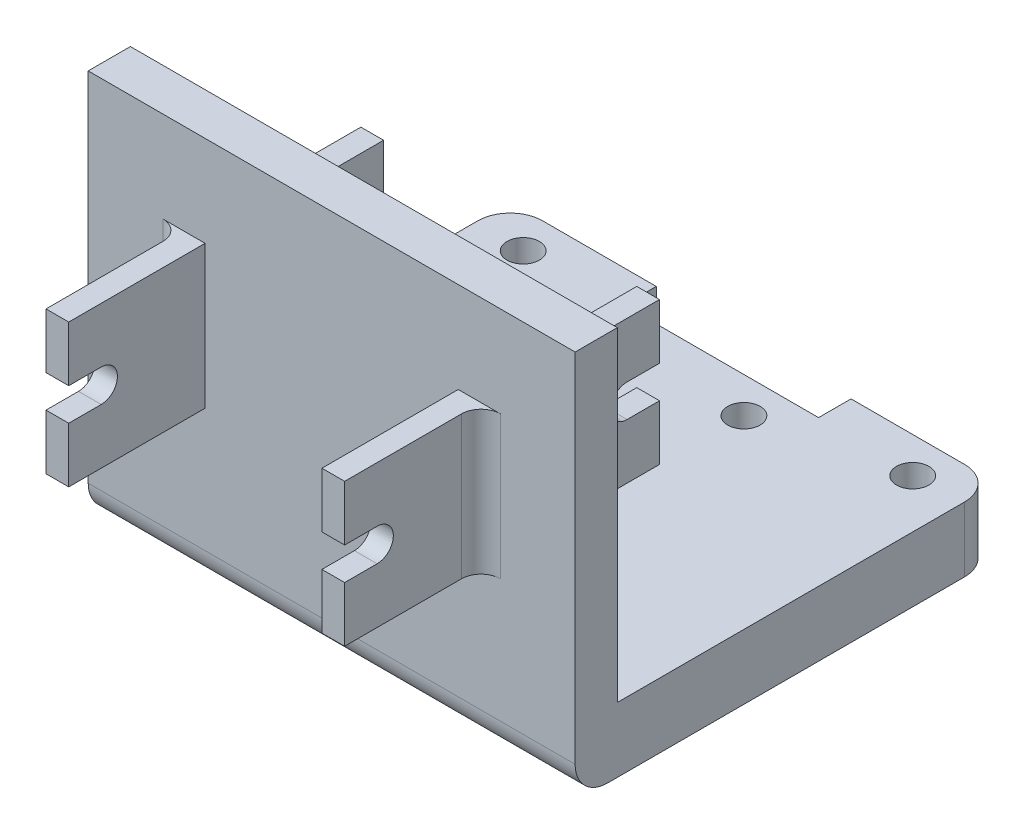
SolidWorks part; units mm, degrees
ref_plane "Front Plane" through (0, 0, 0) normal (0, 0, 1) x (1, 0, 0)
ref_plane "Top Plane" through (0, 0, 0) normal (0, 1, 0) x (1, 0, 0)
ref_plane "Right Plane" through (0, 0, 0) normal (1, 0, 0) x (0, 0, -1)
sketch "Sketch1" plane through (0, 0, 0) normal (0, 1, 0) x (1, 0, 0)
  line L1 (-37.5, -27.5) -> (37.5, -27.5)
  line L2 (-37.5, -27.5) -> (-37.5, 27.5)
  line L3 (-37.5, 27.5) -> (37.5, 27.5)
  line L4 (37.5, -27.5) -> (37.5, 27.5)
  line L5 (-37.5, -27.5) -> (37.5, 27.5) construction
  line L6 (-37.5, 27.5) -> (37.5, -27.5) construction
  circle A0 centre (-30, 22) radius 2.5
  circle A1 centre (30, 22) radius 2.5
  circle A2 centre (0, -18) radius 2.5
  point P0 (0, 0)
  dimension "D3" = 5
  dimension "D4" = 5
  dimension "D5" = 5
  dimension "D1" = 75
  dimension "D2" = 55
  dimension "D6" = 7.5
  dimension "D7" = 7.5
  dimension "D8" = 30
  dimension "D9" = 40
extrude "Boss-Extrude1" add sketch "Sketch1" along normal blind 10 contours L3 L4 L1 L2
sketch "Sketch7" plane through (0, 0, 0) normal (0, 1, 0) x (1, 0, 0)
  line L5 (-37.5, -27.5) -> (37.5, -27.5)
  line L6 (-37.5, -27.5) -> (-37.5, -37.5)
  line L7 (-37.5, -37.5) -> (37.5, -37.5)
  line L8 (37.5, -27.5) -> (37.5, -37.5)
  dimension "D1" = 10
  dimension "D2" = 75
extrude "Boss-Extrude2" add sketch "Sketch7" along normal blind 60
sketch "Sketch9" plane through (0, 60, 0) normal (0, 1, 0) x (1, 0, 0)
  line L0 (37.5, -37.5) -> (37.5, -27.5) construction
  line L1 (-37.5, -27.5) -> (37.5, -27.5)
  line L2 (-37.5, -27.5) -> (-37.5, -31)
  line L3 (-37.5, -31) -> (37.5, -31)
  line L4 (37.5, -27.5) -> (37.5, -31)
  dimension "D1" = 3.5
extrude "Cut-Extrude5" cut sketch "Sketch9" against normal blind 50
fillet "Fillet3" radius 5 1 edges at (0, 0, 37.5)
fillet "Fillet4" radius 5 2 edges at (37.5, 5, -27.5) (-37.5, 5, -27.5)
sketch "Sketch10" plane through (0, 0, 37.5) normal (0, 0, 1) x (1, 0, 0)
  line L1 (-23, 50) -> (23, 50)
  line L2 (-23, 50) -> (-23, 20)
  line L3 (-23, 20) -> (23, 20)
  line L4 (23, 50) -> (23, 20)
  line L5 (-37.5, 60) -> (-37.5, 5) construction
  line L6 (-37.5, 60) -> (37.5, 60) construction
  point P6 (0, 50)
  dimension "D1" = 30
  dimension "D2" = 46
  dimension "D3" = 37.5
  dimension "D4" = 10
extrude "Boss-Extrude3" add sketch "Sketch10" along normal blind 21
sketch "Sketch11" plane through (0, 50, 0) normal (0, 1, 0) x (1, 0, 0)
  line L0 (-37.5, -37.5) -> (37.5, -37.5) construction
  line L1 (-18, -37.5) -> (18, -37.5)
  line L2 (-18, -37.5) -> (-18, -53.5)
  line L3 (-18, -53.5) -> (18, -53.5)
  line L4 (18, -37.5) -> (18, -53.5)
  line L5 (-23, -58.5) -> (-23, -37.5) construction
  point P6 (0, -37.5)
  dimension "D1" = 36
  dimension "D2" = 23
  dimension "D3" = 16
extrude "Cut-Extrude6" cut sketch "Sketch11" against normal through all
sketch "Sketch12" plane through (0, 0, 31) normal (0, 0, -1) x (-1, 0, 0)
  line L1 (-23, 50) -> (23, 50)
  line L2 (-23, 50) -> (-23, 20)
  line L3 (-23, 20) -> (23, 20)
  line L4 (23, 50) -> (23, 20)
  line L6 (37.5, 60) -> (-37.5, 60) construction
  line L8 (-37.5, 10) -> (-37.5, 60) construction
  point P8 (0, 50)
  dimension "D1" = 46
  dimension "D2" = 30
  dimension "D3" = 10
  dimension "D4" = 37.5
extrude "Boss-Extrude4" add sketch "Sketch12" along normal blind 21
sketch "Sketch14" plane through (0, 50, 0) normal (0, 1, 0) x (1, 0, 0)
  line L0 (-23, -31) -> (23, -31) construction
  line L1 (-18, -31) -> (18, -31)
  line L2 (-18, -31) -> (-18, -15)
  line L3 (-18, -15) -> (18, -15)
  line L4 (18, -31) -> (18, -15)
  line L5 (-23, -10) -> (-23, -31) construction
  dimension "D1" = 36
  dimension "D2" = 5
  dimension "D3" = 16
extrude "Cut-Extrude7" cut sketch "Sketch14" against normal up to next
sketch "Sketch15" plane through (0, 0, 0) normal (0, -1, 0) x (1, 0, 0)
  line L0 (-15, -22.5) -> (-3, -22.5)
  line L1 (-15, -22.5) -> (-15, -27.5)
  line L2 (32.5, -27.5) -> (-32.5, -27.5) construction
  line L3 (15, -22.5) -> (15, -27.5)
  line L4 (-3, -22.5) -> (-3, -27.5)
  line L5 (3, -22.5) -> (3, -27.5)
  line L6 (-15, -27.5) -> (-3, -27.5)
  line L7 (3, -27.5) -> (15, -27.5)
  line L8 (3, -22.5) -> (15, -22.5)
  circle A0 centre (-30, -22) radius 2.5 construction
  circle A1 centre (30, -22) radius 2.5 construction
  point P14 (0, -27.5)
  dimension "D1" = 15
  dimension "D2" = 5
  dimension "D3" = 3
  dimension "D4" = 3
  dimension "D5" = 15
extrude "Boss-Extrude5" add sketch "Sketch15" along normal blind 20
sketch "Sketch16" plane through (0, 50, 0) normal (0, 1, 0) x (1, 0, 0)
  line L0 (-19.5, -31) -> (-19.5, -12.8854)
  line L1 (-23, -31) -> (-18, -31) construction
  line L2 (-19.5, -12.8854) -> (-19.5, -10)
  line L3 (-23, -10) -> (23, -10) construction
  line L4 (-19.5, -10) -> (19.5, -9.8969)
  line L5 (19.5, -9.8969) -> (19.5, -31)
  line L6 (23, -10) -> (23, -31) construction
  line L7 (19.5, -31) -> (-19.5, -31)
  line L8 (-23, -10) -> (-23, -31) construction
  line L9 (-33.2343, -34.25) -> (29.1707, -34.25)
  line L10 (-37.5, -31) -> (37.5, -31) construction
  line L14 (19.5, -58.6031) -> (19.5, -37.5)
  line L15 (-19.5, -58.5) -> (19.5, -58.6031)
  line L16 (-19.5, -55.6146) -> (-19.5, -58.5)
  line L17 (-19.5, -37.5) -> (-19.5, -55.6146)
  line L18 (19.5, -37.5) -> (-19.5, -37.5)
  dimension "D1" = 3.5
  dimension "D2" = 21.1031
  dimension "D3" = 3.5
  dimension "D4" = 3.25
extrude "Cut-Extrude9" cut sketch "Sketch16" along direction (0, -1, 0) on the side against the normal up to next (30 mm away) contours L14 L18 L17 L16 L15 | L7 L0 L2 L4 L5
sketch "Sketch17" plane through (-23, 0, 0) normal (-1, 0, 0) x (0, 0, 1)
  line L0 (10, 24) -> (31, 24)
  line L1 (10, 20) -> (10, 50) construction
  line L2 (31, 20) -> (31, 50) construction
  line L3 (10, 46) -> (31, 46)
  line L4 (10, 50) -> (31, 50) construction
  line L5 (10, 20) -> (31, 20) construction
  line L6 (15, 37.5) -> (10, 37.5)
  line L7 (15, 32.5) -> (10, 32.5)
  line L8 (10, 37.5) -> (10, 32.5)
  line L9 (10, 46) -> (10, 50)
  line L10 (10, 50) -> (31, 50)
  line L11 (31, 10) -> (31, 60) construction
  line L12 (10, 50) -> (31, 50) construction
  line L13 (31, 50) -> (31, 46)
  line L14 (31, 24) -> (31, 20)
  line L15 (31, 20) -> (10, 20)
  line L16 (10, 20) -> (10, 24)
  line L17 (34.25, 60) -> (34.25, 0)
  line L18 (37.5, 60) -> (31, 60) construction
  line L19 (37.5, 24) -> (37.5, 20)
  line L20 (37.5, 20) -> (58.5, 20)
  line L21 (58.5, 20) -> (58.5, 24)
  line L22 (58.5, 24) -> (37.5, 24)
  line L23 (58.5, 37.5) -> (58.5, 32.5)
  line L24 (53.5, 32.5) -> (58.5, 32.5)
  line L25 (53.5, 37.5) -> (58.5, 37.5)
  line L26 (58.5, 46) -> (58.5, 50)
  line L27 (58.5, 50) -> (37.5, 50)
  line L28 (37.5, 50) -> (37.5, 46)
  line L29 (58.5, 46) -> (37.5, 46)
  arc A0 (15, 32.5) -> (15, 37.5) centre (15, 35) ccw
  arc A1 (53.5, 32.5) -> (53.5, 37.5) centre (53.5, 35) cw
  line M14 (31, 20) -> (31, 50)
  line M15 (31, 50) -> (10, 50)
  line M16 (10, 50) -> (10, 20)
  line M17 (10, 20) -> (31, 20)
  dimension "D3" = 5
  dimension "D1" = 4
  dimension "D2" = 4
  dimension "D4" = 5
  dimension "D5" = 15
extrude "Cut-Extrude10" cut sketch "Sketch17" against normal through all contours L29 L26 L27 L28 | A1 L24 L23 L25 | L21 L22 L19 L20 | L3 M16 M14 M15 | L7 A0 L6 M16 | L0 M16 M17 M14
fillet "Fillet5" radius 3 4 edges at (-23, 35, 37.5) (23, 35, 37.5) (23, 35, 31) (-23, 35, 31)
sketch "Sketch18" plane through (0, 0, -27.5) normal (0, 0, -1) x (-1, 0, 0)
  line L0 (-15, -20) -> (-15, 10)
  line L1 (-32.5, 10) -> (32.5, 10) construction
  line L2 (15, -20) -> (15, 10)
  line L3 (15, 10) -> (-15, 10)
  line L4 (-15, -20) -> (15, -20)
extrude "Cut-Extrude11" cut sketch "Sketch18" against normal blind 5
sketch "Sketch19" plane through (0, 10, 0) normal (0, 1, 0) x (1, 0, 0)
  line L0 (-15, 22.5) -> (-15, 8.7295)
  line L1 (15, 22.5) -> (15, 8.7295)
  line L2 (-15, 22.5) -> (15, 22.5) construction
  circle A0 centre (-9, 17) radius 2.5
  circle A1 centre (9, 17) radius 2.5
  point P12 (0, 0)
  dimension "D1" = 5
  dimension "D2" = 5
  dimension "D4" = 6
  dimension "D5" = 5.5
  dimension "D3" = 6
  dimension "D6" = 5.5
extrude "Cut-Extrude12" cut sketch "Sketch19" against normal through all contours A1 | A0
